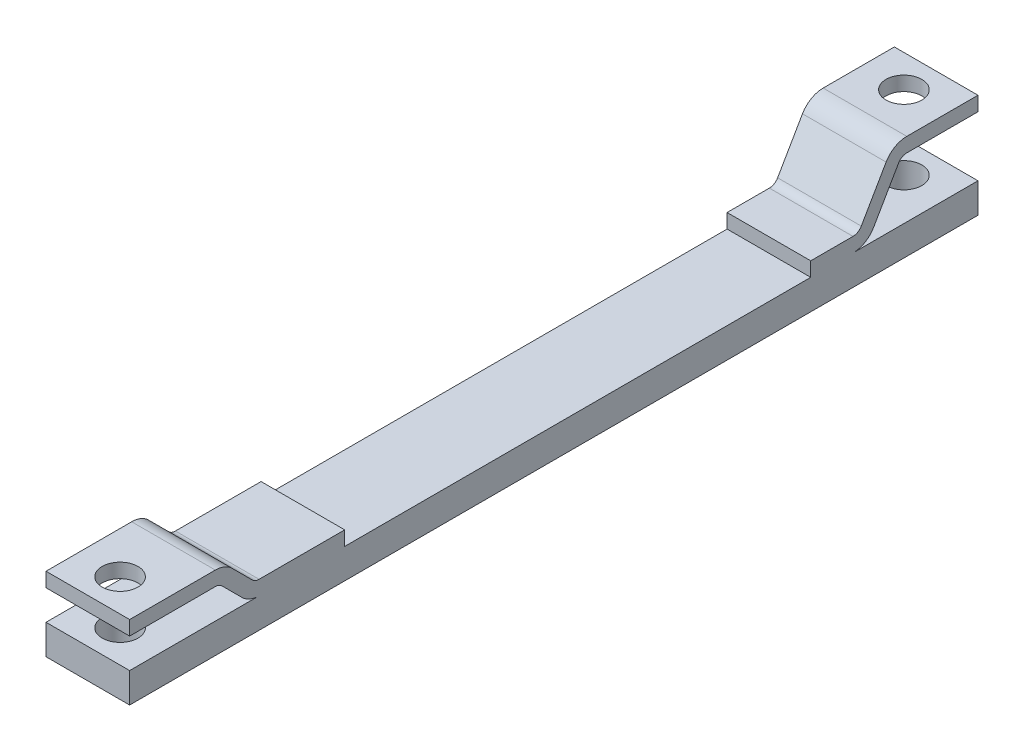
SolidWorks part; units mm, degrees
ref_plane "Front Plane" through (0, 0, 0) normal (0, 0, 1) x (1, 0, 0)
ref_plane "Top Plane" through (0, 0, 0) normal (0, 1, 0) x (1, 0, 0)
ref_plane "Right Plane" through (0, 0, 0) normal (1, 0, 0) x (0, 0, -1)
sketch "Sketch1" plane through (0, 0, 0) normal (1, 0, 0) x (0, 0, -1)
  line L1 (108.3137, 25) -> (108.2843, 25)
  line L2 (108.3137, 25) -> (0, 25)
  line L40 (0, 25) -> (0, 0)
  line L41 (0, 0) -> (710, 0)
  line L42 (710, 0) -> (710, 25)
  line L43 (710, 25) -> (605.3812, 25)
  line L44 (622.7017, 35) -> (643.4863, 71)
  line L45 (650.4145, 75) -> (710, 75)
  line L46 (710, 75) -> (710, 87)
  line L47 (710, 87) -> (650.4145, 87)
  line L48 (633.094, 77) -> (612.3094, 41)
  line L49 (605.3812, 37) -> (570, 37)
  line L50 (570, 37) -> (570, 25)
  line L51 (570, 25) -> (180, 25)
  line L52 (180, 25) -> (180, 37)
  line L53 (180, 37) -> (108.3137, 37)
  line L54 (102.6569, 39.3431) -> (85.8579, 56.1421)
  line L55 (71.7157, 62) -> (0, 62)
  line L56 (0, 62) -> (0, 50)
  line L57 (0, 50) -> (71.6863, 50)
  line L58 (77.3431, 47.6569) -> (94.1421, 30.8579)
  line L59 (108.3137, 25) -> (108.2843, 25)
  arc A0 (108.3137, 37) -> (102.6569, 39.3431) centre (108.3137, 45) cw
  arc A1 (71.6863, 50) -> (77.3431, 47.6569) centre (71.6863, 42) cw
  arc A2 (605.3812, 37) -> (612.3094, 41) centre (605.3812, 45) ccw
  arc A3 (650.4145, 75) -> (643.4863, 71) centre (650.4145, 67) ccw
  arc A4 (650.4145, 87) -> (633.094, 77) centre (650.4145, 67) ccw
  arc A5 (622.7017, 35) -> (605.3812, 25) centre (605.3812, 45) cw
  arc A6 (71.7157, 62) -> (85.8579, 56.1421) centre (71.7157, 42) cw
  arc A7 (108.2843, 25) -> (94.1421, 30.8579) centre (108.2843, 45) cw
  point P39 (80, 62)
  dimension "D6" = 8
  dimension "D15" = 20
  dimension "D1" = 710
  dimension "D2" = 25
  dimension "D3" = 25
  dimension "D4" = 12
  dimension "D5" = 180
  dimension "D7" = 80
  dimension "D8" = 45
  dimension "D9" = 12
  dimension "D10" = 140
  dimension "D11" = 62
  dimension "D12" = 12
  dimension "D13" = 60
  dimension "D14" = 12
  dimension "D16" = 35.3812
extrude "Boss-Extrude1" add sketch "Sketch1" along normal blind 70
sketch "Sketch2" plane through (0, 0, 0) normal (0, 1, 0) x (1, 0, 0)
  line L1 (70, 710) -> (0, 710) construction
  line L2 (70, 0) -> (0, 0) construction
  circle A1 centre (35, 683) radius 15
  circle A2 centre (35, 27) radius 15
  point P9 (35, 710)
  dimension "D1" = 30
  dimension "D4" = 30
  dimension "D2" = 27
  dimension "D3" = 27
extrude "Cut-Extrude1" cut sketch "Sketch2" along normal through all
